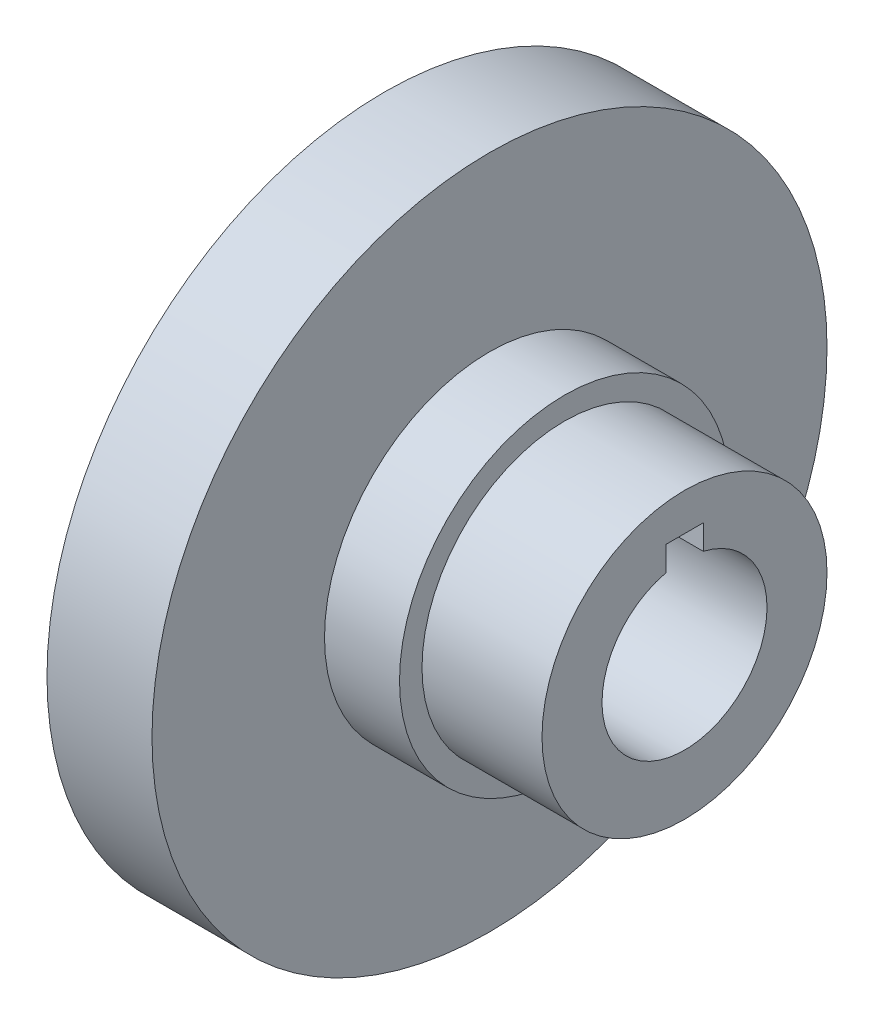
SolidWorks part; units mm, degrees
ref_plane "前视基准面" through (0, 0, 0) normal (0, 0, 1) x (1, 0, 0)
ref_plane "上视基准面" through (0, 0, 0) normal (0, 1, 0) x (1, 0, 0)
ref_plane "右视基准面" through (0, 0, 0) normal (1, 0, 0) x (0, 0, -1)
sketch "草图1" plane through (0, 0, 0) normal (1, 0, 0) x (0, 0, -1)
  circle A0 centre (0, 0) radius 45
extrude "凸台-拉伸1" add sketch "草图1" along normal blind 14
sketch "草图2" plane through (14, 0, 0) normal (1, 0, 0) x (0, 0, -1)
  circle A0 centre (0, 0) radius 22
extrude "凸台-拉伸2" add sketch "草图2" along normal blind 10
sketch "草图3" plane through (24, 0, 0) normal (1, 0, 0) x (0, 0, -1)
  circle A0 centre (0, 0) radius 19
extrude "凸台-拉伸3" add sketch "草图3" along normal blind 16
sketch "草图4" plane through (0, 0, 0) normal (-1, 0, 0) x (0, 0, 1)
  circle A0 centre (0, 0) radius 23
extrude "切除-拉伸1" cut sketch "草图4" against normal blind 12
sketch "草图5" plane through (12, 0, 0) normal (-1, 0, 0) x (0, 0, 1)
  circle A0 centre (0, 0) radius 11
extrude "切除-拉伸2" cut sketch "草图5" against normal through all
sketch "草图6" plane through (0, 0, 0) normal (0, 0, 1) x (1, 0, 0)
  line L0 (40, 0) -> (12, 0)
  line L1 (40, -19) -> (40, 19) construction
  line L2 (12, 23) -> (12, -23) construction
  line L3 (12, 0) -> (12, 14)
  line L4 (12, 14) -> (40, 14)
  line L5 (40, 14) -> (40, 0)
  dimension "D1" = 14
extrude "切除-拉伸3" cut sketch "草图6" against normal mid plane 5
sketch "草图7" plane through (0, 0, 0) normal (-1, 0, 0) x (0, 0, 1)
  line L0 (-23, 0) -> (-45, 0)
  circle A0 centre (0, 0) radius 23 construction
  circle A1 centre (0, 0) radius 45 construction
  circle A2 centre (-34, 0) radius 4
  circle A3 centre (0, 34) radius 4
  circle A4 centre (34, 0) radius 4
  circle A5 centre (0, -34) radius 4
  dimension "D1" = 4
extrude "切除-拉伸4" cut sketch "草图7" against normal blind 12 contours A3 | A4 | A5 | L0 A2 | L0 A2
fillet "圆角1" radius 3 1 edges at (12, 0, 23)
